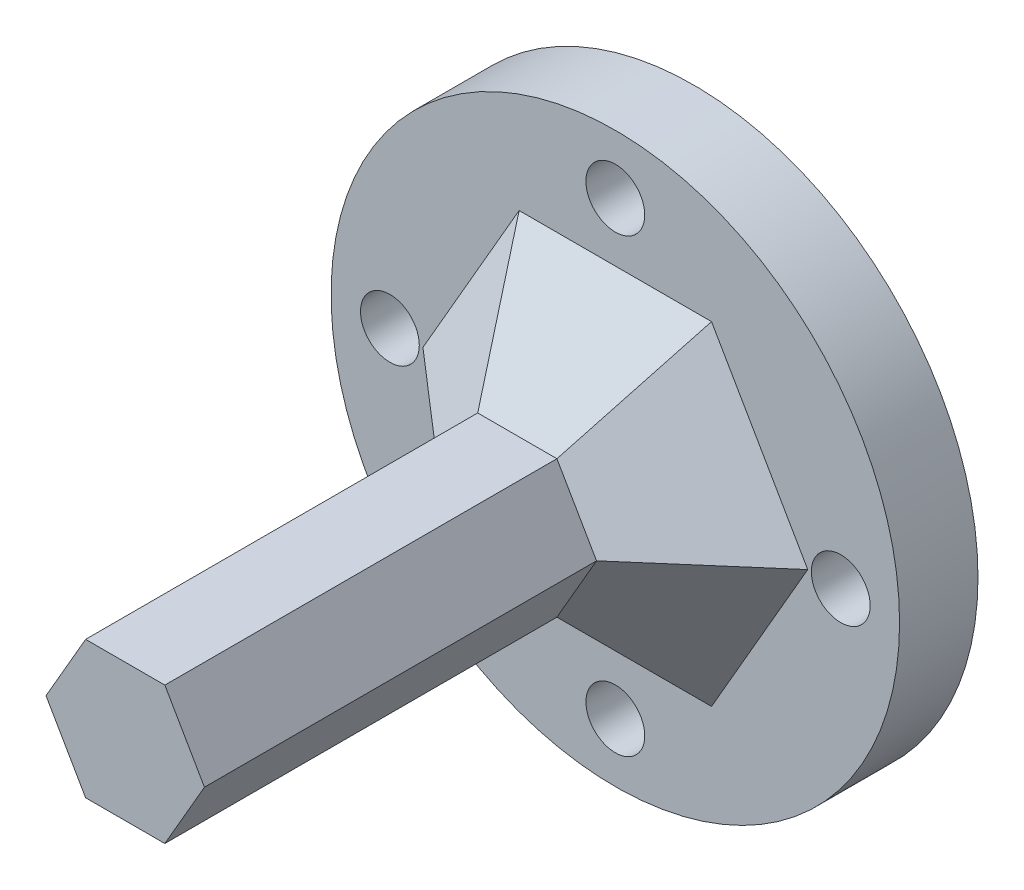
SolidWorks part; units mm, degrees
ref_plane "Front Plane" through (0, 0, 0) normal (0, 0, 1) x (1, 0, 0)
ref_plane "Top Plane" through (0, 0, 0) normal (0, 1, 0) x (1, 0, 0)
ref_plane "Right Plane" through (0, 0, 0) normal (1, 0, 0) x (0, 0, -1)
sketch "Sketch1" plane through (0, 0, 0) normal (0, 0, 1) x (1, 0, 0)
  circle A2 centre (43.4831, -58.4891) radius 1.5
  circle A3 centre (43.4831, -58.4891) radius 1.5
  circle A5 centre (54.9831, -69.9891) radius 1.5
  circle A6 centre (54.9831, -69.9891) radius 1.5
  circle A8 centre (31.9831, -69.9891) radius 1.5
  circle A9 centre (31.9831, -69.9891) radius 1.5
  circle A11 centre (43.4831, -81.4891) radius 1.5
  circle A12 centre (43.4831, -81.4891) radius 1.5
  circle A15 centre (43.4831, -69.9891) radius 14.5
  circle A16 centre (43.4831, -69.9891) radius 14.5
  dimension "D1" = 0
  dimension "D2" = 0
  dimension "D3" = 0
  dimension "D4" = 0
  dimension "D5" = 0
extrude "Boss-Extrude1" add sketch "Sketch1" along normal blind 4
sketch "Sketch2" plane through (0, 0, 4) normal (0, 0, 1) x (1, 0, 0)
  line L1 (47.5246, -69.9891) -> (45.5039, -66.4891)
  line L2 (45.5039, -66.4891) -> (41.4624, -66.4891)
  line L3 (41.4624, -66.4891) -> (39.4417, -69.9891)
  line L4 (39.4417, -69.9891) -> (41.4624, -73.4891)
  line L5 (41.4624, -73.4891) -> (45.5039, -73.4891)
  line L6 (45.5039, -73.4891) -> (47.5246, -69.9891)
  circle A0 centre (43.4831, -69.9891) radius 3.5 construction
  dimension "D1" = 7
extrude "Boss-Extrude2" add sketch "Sketch2" along normal blind 25
chamfer "Chamfer1" distance 5 angle 45 6 edges at (40.4521, -68.2391, 4) (43.4831, -66.4891, 4) (46.5142, -68.2391, 4) (46.5142, -71.7391, 4) (43.4831, -73.4891, 4) (40.4521, -71.7391, 4)
